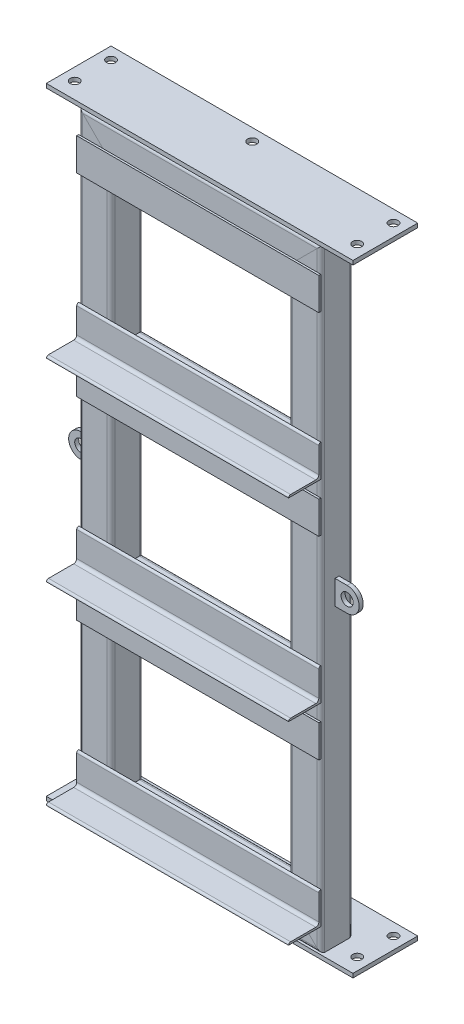
SolidWorks part; units mm, degrees
material "Plain Carbon Steel"
ref_plane "Front Plane" through (0, 0, 0) normal (0, 0, 1) x (1, 0, 0)
ref_plane "Top Plane" through (0, 0, 0) normal (0, 1, 0) x (1, 0, 0)
ref_plane "Right Plane" through (0, 0, 0) normal (1, 0, 0) x (0, 0, -1)
sketch "Sketch1" plane through (0, 0, 0) normal (0, 0, 1) x (1, 0, 0)
  line L0 (-165.1, 0) -> (165.1, 0)
  line L1 (165.1, -457.2) -> (-165.1, -457.2)
  line L2 (165.1, -457.2) -> (165.1, 457.2)
  line L3 (165.1, 457.2) -> (-165.1, 457.2)
  line L4 (-165.1, -457.2) -> (-165.1, 457.2)
  line L5 (165.1, -457.2) -> (-165.1, 457.2) construction
  line L6 (165.1, 457.2) -> (-165.1, -457.2) construction
  line L7 (-165.1, 152.4) -> (165.1, 152.4)
  line L8 (-165.1, -152.4) -> (165.1, -152.4)
  line L9 (-165.1, 457.2) -> (165.1, 152.4) construction
  line L10 (-165.1, 152.4) -> (165.1, -152.4) construction
  line L11 (-165.1, -152.4) -> (165.1, -457.2) construction
  point P0 (0, 0)
  dimension "D1" = 914.4
  dimension "D2" = 330.2
other "Structural Member1"
ref_plane "Plane1" through (-165.1, -457.2, 0) normal (0, 1, 0) x (-1, 0, 0)
sketch "Sketch11" plane through (-165.1, -457.2, 0) normal (0, 1, 0) x (-1, 0, 0)
  line L0 (-19.304, -22.352) -> (19.304, -22.352)
  line L1 (-22.352, -19.304) -> (-22.352, 19.304)
  line L2 (19.304, 22.352) -> (-19.304, 22.352)
  line L3 (22.352, 19.304) -> (22.352, -19.304)
  line L4 (-19.304, -25.4) -> (19.304, -25.4)
  line L5 (-25.4, -19.304) -> (-25.4, 19.304)
  line L6 (19.304, 25.4) -> (-19.304, 25.4)
  line L7 (25.4, 19.304) -> (25.4, -19.304)
  line L8 (0, 0) -> (22.352, 0) construction
  line L9 (0, 0) -> (0, 22.352) construction
  arc A0 (25.4, 19.304) -> (19.304, 25.4) centre (19.304, 19.304) ccw
  arc A1 (19.304, -25.4) -> (25.4, -19.304) centre (19.304, -19.304) ccw
  arc A2 (-25.4, -19.304) -> (-19.304, -25.4) centre (-19.304, -19.304) ccw
  arc A3 (-19.304, 25.4) -> (-25.4, 19.304) centre (-19.304, 19.304) ccw
  arc A4 (-19.304, 22.352) -> (-22.352, 19.304) centre (-19.304, 19.304) ccw
  arc A5 (22.352, 19.304) -> (19.304, 22.352) centre (19.304, 19.304) ccw
  arc A6 (19.304, -22.352) -> (22.352, -19.304) centre (19.304, -19.304) ccw
  arc A7 (-22.352, -19.304) -> (-19.304, -22.352) centre (-19.304, -19.304) ccw
  point P3 (0, 25.4)
  point P4 (25.4, 0)
  point P5 (0, -25.4)
  point P6 (-25.4, 0)
  point P7 (-25.4, 25.4)
  point P8 (-25.4, -25.4)
  point P33 (0, 0)
  point P35 (25.4, -25.4)
  point P36 (25.4, 25.4)
  point P37 (0, 0)
  dimension "D1" = 6.096
  dimension "Thickness" = 3.048
  dimension "V_leg" = 50.8
sketch "Sketch12" plane through (0, 482.6, 0) normal (0, 1, 0) x (1, 0, 0)
  line L1 (241.3, -25.665) -> (241.3, -76.2) construction
  line L2 (-241.3, -25.665) -> (-241.3, 76.2)
  line L3 (-241.3, 76.2) -> (241.3, 76.2)
  line L4 (241.3, -25.665) -> (241.3, 76.2)
  line L5 (-241.3, -76.2) -> (241.3, 76.2) construction
  line L6 (-241.3, 76.2) -> (241.3, -76.2) construction
  line L7 (184.404, 25.4) -> (-184.404, 25.4) construction
  line L8 (-190.5, -19.304) -> (-190.5, 19.304) construction
  line L9 (-241.3, -25.665) -> (241.3, -25.665)
  line L10 (-222.25, -57.15) -> (222.25, -57.15) construction
  line L11 (-222.25, -57.15) -> (-222.25, 57.15) construction
  line L12 (-222.25, 57.15) -> (222.25, 57.15) construction
  line L13 (222.25, -57.15) -> (222.25, 57.15) construction
  line L14 (-222.25, -57.15) -> (222.25, 57.15) construction
  line L15 (-222.25, 57.15) -> (222.25, -57.15) construction
  line L16 (241.3, -76.2) -> (-241.3, -76.2) construction
  line L17 (-241.3, -76.2) -> (-241.3, -25.665) construction
  point P9 (0, 57.15)
  point P10 (-222.25, 0)
  point P11 (0, -57.15)
  point P12 (222.25, 0)
  point P25 (0, 0)
  dimension "D3" = 19.05
  dimension "D1" = 50.8
  dimension "D2" = 50.8
  dimension "D4" = 19.05
extrude "Boss-Extrude1" add sketch "Sketch12" along normal blind 6.35 separate body
hole_wizard "9/16 (0.5625) Diameter Hole1" positions "Sketch14" profile "Sketch13" hole size "9/16" standard "Ansi Inch"
sketch "Sketch14" plane through (0, 488.95, 0) normal (0, 1, 0) x (-1, 0, 0)
  point P1 (222.25, -57.15)
  point P4 (222.25, 0)
  point P16 (-222.25, 0)
  point P19 (-222.25, -57.15)
  point P22 (0, -57.15)
sketch "Sketch13" plane through (-222.25, 488.95, -57.15) normal (1, 0, 0) x (0, 0, 1)
  line L0 (0, 0) -> (0, 85.3184)
  line L1 (0, 85.3184) -> (7.1437, 81.026)
  line L2 (7.1437, 81.026) -> (7.1437, 0)
  line L5 (7.1437, 0) -> (0, 0)
  line L10 (0, 85.3184) -> (-7.1438, 81.026) construction
  line L11 (0, -6.35) -> (0, 107.95) construction
  dimension "Hole Dia." = 14.2875
  dimension "Hole Depth" = 81.026
  dimension "Drill Angle" = 118
mirror "Mirror1" about plane through (0, 0, 0) normal (0, 1, 0) of bodies 109
ref_plane "BracketPlane" through (0, 0, 25.4) normal (0, 0, 1) x (1, 0, 0)
sketch "Sketch15" plane through (0, 0, 25.4) normal (0, 0, 1) x (1, 0, 0)
  line L0 (0, -476.504) -> (0, 476.504) construction
  line L1 (-184.404, -476.504) -> (184.404, -476.504) construction
  line L2 (184.404, 476.504) -> (-184.404, 476.504) construction
  line L3 (139.7, 431.8) -> (-139.7, 177.8) construction
  line L4 (-139.7, -127) -> (139.7, -127) construction
  line L5 (-139.7, -127) -> (-139.7, 127) construction
  line L6 (-139.7, 127) -> (139.7, 127) construction
  line L7 (139.7, -127) -> (139.7, 127) construction
  line L8 (139.7, 431.8) -> (-139.7, 431.8) construction
  line L9 (139.7, 431.8) -> (139.7, 177.8) construction
  line L10 (139.7, 177.8) -> (-139.7, 177.8) construction
  line L11 (-139.7, 431.8) -> (-139.7, 177.8) construction
  line L12 (139.7, -177.8) -> (-139.7, -177.8) construction
  line L13 (139.7, -177.8) -> (139.7, -431.8) construction
  line L14 (139.7, -431.8) -> (-139.7, -431.8) construction
  line L15 (-139.7, -177.8) -> (-139.7, -431.8) construction
  line L16 (139.7, 127) -> (-139.7, -127) construction
  line L17 (139.7, -177.8) -> (-139.7, -431.8) construction
  line L18 (-190.5, 444.5) -> (190.5, 444.5)
  line L19 (-190.5, 482.6) -> (-190.5, -482.6) construction
  line L20 (190.5, -482.6) -> (190.5, 482.6) construction
  line L21 (-190.5, 165.1) -> (0, 165.1)
  line L22 (-190.5, 165.1) -> (190.5, 165.1)
  circle A0 centre (0, 304.8) radius 139.7 construction
  circle A1 centre (0, 0) radius 139.7 construction
  circle A2 centre (0, -304.8) radius 139.7 construction
  dimension "D1" = 279.4
other "Structural Member2"
ref_plane "Plane4" through (-190.5, 165.1, 25.4) normal (1, 0, 0) x (0, 1, 0)
sketch "Sketch141" plane through (-190.5, 165.1, 25.4) normal (1, 0, 0) x (0, 1, 0)
  line L0 (0, 0) -> (0, 50.8)
  line L1 (0, 50.8) -> (0.0051, 50.8)
  line L2 (3.175, 47.6301) -> (3.175, 7.9375)
  line L3 (7.9375, 3.175) -> (47.6301, 3.175)
  line L4 (50.8, 0.0051) -> (50.8, 0)
  line L5 (50.8, 0) -> (0, 0)
  arc A0 (50.8, 0.0051) -> (47.6301, 3.175) centre (47.6301, 0.0051) ccw
  arc A1 (0.0051, 50.8) -> (3.175, 47.6301) centre (0.0051, 47.6301) cw
  arc A2 (7.9375, 3.175) -> (3.175, 7.9375) centre (7.9375, 7.9375) cw
  point P10 (25.4, 0)
  point P14 (0, 25.4)
  point P15 (3.175, 25.4)
  point P16 (25.4, 3.175)
  point P17 (3.175, 50.8)
  point P18 (50.8, 3.175)
  point P19 (0, 0)
  dimension "D2" = 0.0051
  dimension "Radius_1" = 4.7625
  dimension "D1" = 3.175
  dimension "H_leg" = 50.8
sketch "Sketch142" plane through (190.5, 0, 0) normal (1, 0, 0) x (0, 0, -1)
  line L1 (-25.4, 444.5) -> (-28.575, 444.5)
  line L2 (-25.4, 444.5) -> (-25.4, 393.7)
  line L3 (-25.4, 393.7) -> (-28.575, 393.7)
  line L4 (-28.575, 444.5) -> (-28.575, 393.7)
  dimension "D1" = 3.175
  dimension "D2" = 50.8
extrude "Boss-Extrude2" add sketch "Sketch142" against normal up to surface (381 mm away) separate body up to face at (-190.5, 0, 0)
pattern_linear "LPattern1" count 3 spacing 304.8 along (0, -1, 0) of bodies 112 113 111
sketch "Sketch144" plane through (0, 0, 0) normal (0, 0, 1) x (1, 0, 0)
  line L0 (0, 0) -> (190.5, 0) construction
  line L1 (190.5, -482.6) -> (190.5, 482.6) construction
  line L2 (190.5, 0) -> (228.6, 0) construction
  line L3 (209.55, 19.05) -> (190.5, 19.05)
  line L4 (190.5, 19.05) -> (190.5, -19.05)
  line L5 (190.5, -19.05) -> (209.55, -19.05)
  arc A0 (209.55, 19.05) -> (209.55, -19.05) centre (209.55, 0) cw
  circle A1 centre (209.55, 0) radius 9.525
  dimension "D2" = 19.05
  dimension "D3" = 19.05
  dimension "D1" = 38.1
extrude "Boss-Extrude3" add sketch "Sketch144" along normal mid plane 6.35 separate body
mirror "Mirror3" about plane through (0, 0, 0) normal (1, 0, 0) of bodies 120
